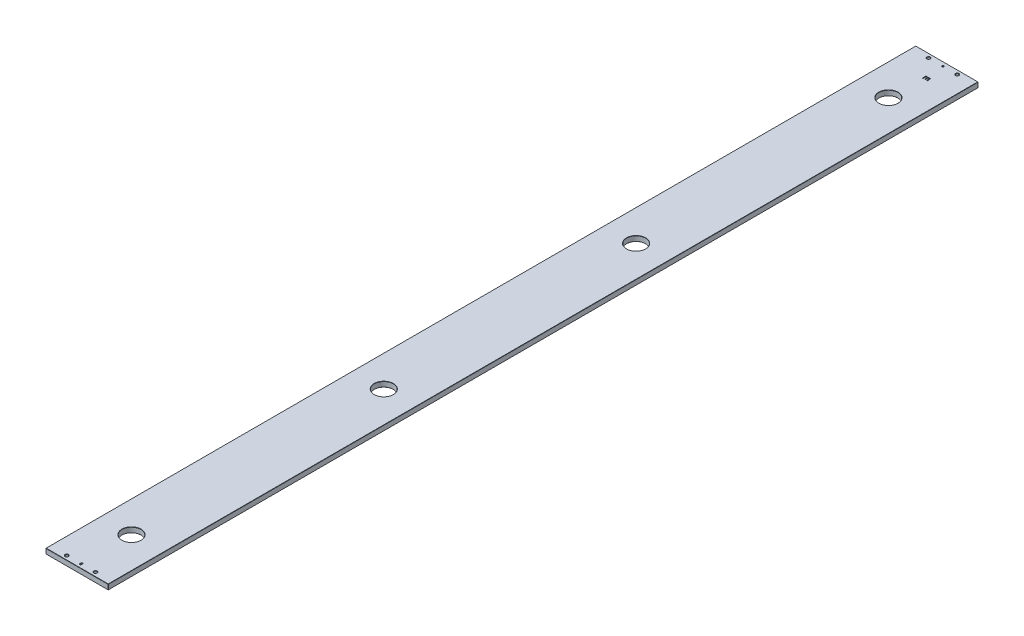
SolidWorks part; units mm, degrees
material "6061 Alloy"
ref_plane "Front" through (0, 0, 0) normal (0, 0, 1) x (1, 0, 0)
ref_plane "Top" through (0, 0, 0) normal (0, 1, 0) x (1, 0, 0)
ref_plane "Right" through (0, 0, 0) normal (1, 0, 0) x (0, 0, -1)
sketch "Sketch1" plane through (0, 0, 0) normal (0, 0, 1) x (1, 0, 0)
  line L0 (-76.2, 0) -> (76.2, 0)
  point P3 (0, 0)
  dimension "D1" = 152.4
extrude "Extrude-Thin1" add sketch "Sketch1" along normal mid plane 2124 thin thin type mid plane wall 12.7
chamfer "Chamfer1" distance 0.5 angle 45 12 edges at (-76.2, -6.35, 0) (0, -6.35, 1062) (76.2, -6.35, 0) (0, -6.35, -1062) (76.2, 6.35, 0) (0, 6.35, 1062) (-76.2, 6.35, 0) (0, 6.35, -1062) (76.2, 0, 1062) (76.2, 0, -1062) (-76.2, 0, -1062) (-76.2, 0, 1062)
sketch "Sketch2" plane through (0, -6.35, 0) normal (0, 1, 0) x (1, 0, 0)
  line L0 (-35, 1052) -> (35, 1052) construction
  line L1 (0, 1061.5) -> (0, 1096.6241) construction
  line L2 (75.7, 1061.5) -> (-75.7, 1061.5) construction
  line L3 (-75.7, 1062) -> (75.7, 1062) construction
  point P9 (0, 1052)
  dimension "D1" = 70
  dimension "D2" = 10
hole_wizard "CBORE for 1/4 Socket Head Cap Screw1" positions "3DSketch1" profile "Sketch3" counterbore size "1/4" standard "Ansi Inch" end condition up to next
sketch3d "3DSketch1"
  point P0 (-35, -6.35, -1052)
  point P3 (35, -6.35, -1052)
sketch "Sketch3" plane through (-35, -6.35, -1052) normal (1, 0, 0) x (0, 0, -1)
  line L0 (0, 0) -> (0, 12.7)
  line L1 (3.5712, 12.065) -> (4.2062, 12.7)
  line L2 (3.5712, 12.065) -> (3.5712, 6.35)
  line L3 (3.5712, 6.35) -> (5.5562, 6.35)
  line L4 (5.5562, 6.35) -> (5.5562, 0)
  line L5 (5.5562, 0) -> (0, 0)
  line L11 (0, -6.35) -> (0, 107.95) construction
  line L12 (4.2062, 12.7) -> (0, 12.7)
  line L13 (-3.5712, 12.065) -> (-4.2062, 12.7) construction
  dimension "Thru Hole Dia." = 7.1425
  dimension "Thru Hole Depth" = 12.7
  dimension "C'Bore Dia." = 11.1125
  dimension "C'Bore Depth" = 6.35
  dimension "Far C'Sink Dia." = 8.4125
  dimension "Far C'Sink Angle" = 90
hole_wizard "1/8 (0.125) Diameter Hole1" positions "3DSketch2" profile "Sketch4" hole size "1/8" standard "Ansi Inch" end condition through all
sketch3d "3DSketch2"
  point P0 (0, -6.35, -1052)
sketch "Sketch4" plane through (0, -6.35, -1052) normal (1, 0, 0) x (0, 0, -1)
  line L0 (0, 0) -> (0, 12.7)
  line L1 (0, 12.7) -> (2.2225, 12.7)
  line L2 (1.6002, 12.0777) -> (1.6002, 0.6223)
  line L3 (1.6002, 0.6223) -> (2.2225, 0)
  line L5 (2.2225, 0) -> (0, 0)
  line L6 (-1.6002, 0.6223) -> (-2.2225, 0) construction
  line L7 (2.2225, 12.7) -> (1.6002, 12.0777)
  line L8 (-2.2225, 12.7) -> (-1.6002, 12.0777) construction
  line L11 (0, -6.35) -> (0, 107.95) construction
  dimension "Thru Hole Dia." = 3.2004
  dimension "Thru Hole Depth" = 12.7
  dimension "Near C'Sink Dia." = 4.445
  dimension "Near C'Sink Angle" = 90
  dimension "Far C'Sink Dia." = 4.445
  dimension "Far C'Sink Angle" = 90
mirror "Mirror1" about plane through (0, 0, 0) normal (0, 0, 1) of "CBORE for 1/4 Socket Head Cap Screw1"
sketch "Sketch5" plane through (0, 6.35, 0) normal (0, 1, 0) x (1, 0, 0)
  line L0 (-35, -1052) -> (35, -1052) construction
  line L1 (0, -1053.5) -> (0, -1050.5) construction
  line L2 (-1.6002, -1053.5) -> (-1.6002, -1050.5)
  line L3 (1.6002, -1053.5) -> (1.6002, -1050.5)
  arc A0 (-1.6002, -1053.5) -> (1.6002, -1053.5) centre (0, -1053.5) ccw
  arc A1 (1.6002, -1050.5) -> (-1.6002, -1050.5) centre (0, -1050.5) ccw
  point P6 (0, -1052)
  dimension "D2" = 1.6002
  dimension "D1" = 3
extrude "Extrude1" cut sketch "Sketch5" against normal up to next
sketch "Sketch6" plane through (0, 6.35, 0) normal (0, 1, 0) x (1, 0, 0)
  line L0 (0, 0) -> (0, 168.0999) construction
  line L1 (0, 0) -> (119.4512, 0) construction
  line L2 (-75.7, 1062) -> (75.7, 1062) construction
  circle A0 centre (0, 919) radius 23
  dimension "D2" = 46
  dimension "D1" = 143
extrude "guide diameter" cut sketch "Sketch6" against normal through all
chamfer "Chamfer2" distance 0.5 angle 45 2 edges at (-23, -6.35, -919) (-23, 6.35, -919)
pattern_linear "LPattern1" count 4 spacing 616 along (0, 0, 1) of "guide diameter", "Chamfer2"
chamfer "Chamfer3" distance 0.5 angle 45 4 edges at (-1.6002, 6.35, 1052) (0, 6.35, 1055.1002) (0, 6.35, 1048.8998) (1.6002, 6.35, 1052)
sketch "Sketch7" plane through (0, 6.35, 0) normal (0, 1, 0) x (1, 0, 0)
  line L0 (0, 1012) -> (0, 985.8298) construction
  line L1 (-75.7, 1062) -> (75.7, 1062) construction
  text T0 "E" font "Arial Rounded MT Bold" height in points 48
  dimension "D1" = 50
extrude "Cut-Extrude1" cut sketch "Sketch7" against normal blind 2
